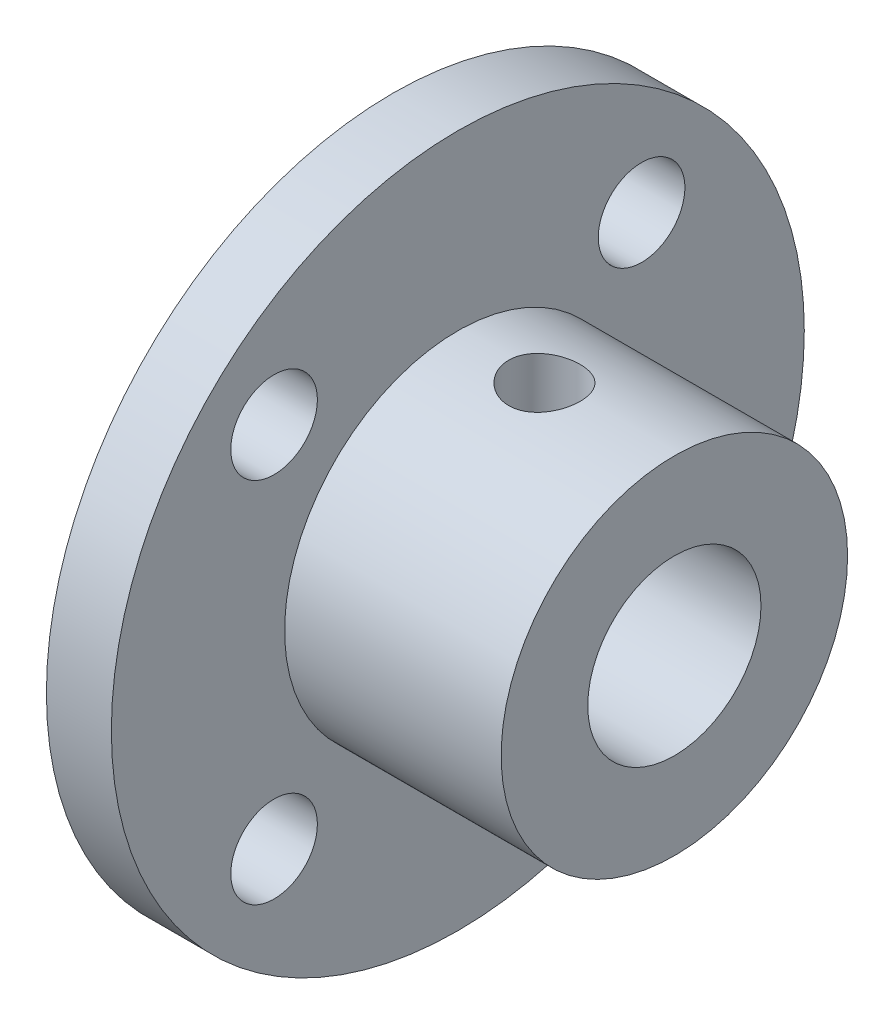
SolidWorks part; units mm, degrees
material "电镀钢"
ref_plane "前视基准面" through (0, 0, 0) normal (0, 0, 1) x (1, 0, 0)
ref_plane "上视基准面" through (0, 0, 0) normal (0, 1, 0) x (1, 0, 0)
ref_plane "右视基准面" through (0, 0, 0) normal (1, 0, 0) x (0, 0, -1)
sketch "草图1" plane through (0, 0, 0) normal (1, 0, 0) x (0, 0, -1)
  circle A0 centre (0, 0) radius 8
  circle A1 centre (0, 0) radius 4
  dimension "D1" = 8
  dimension "D2" = 16
extrude "凸台-拉伸1" add sketch "草图1" along normal blind 10
sketch "草图2" plane through (0, 0, 0) normal (-1, 0, 0) x (0, 0, 1)
  circle A0 centre (0, 0) radius 4
  circle A1 centre (0, 0) radius 16
  dimension "D1" = 32
  dimension "D2" = 8
extrude "凸台-拉伸2" add sketch "草图2" along normal blind 3
sketch "草图3" plane through (0, 0, 0) normal (1, 0, 0) x (0, 0, -1)
  line L0 (0, 0) -> (-8.9538, 8.9538) construction
  line L1 (0, 0) -> (-16.9706, -16.9706) construction
  line L2 (0, 0) -> (-19.7649, 0) construction
  circle A0 centre (-8.4853, -8.4853) radius 2
  circle A1 centre (8.4853, 8.4853) radius 2
  circle A2 centre (-8.4853, 8.4853) radius 2
  circle A3 centre (8.4853, -8.4853) radius 2
  dimension "D2" = 4
  dimension "D3" = 4
  dimension "D1" = 12
  dimension "D4" = 12
  dimension "D5" = 45
  dimension "D6" = 90
extrude "切除-拉伸1" cut sketch "草图3" against normal up to next
hole_wizard "M4 螺纹孔1" positions "草图4" profile "草图5" tap size "M4" standard "GB"
sketch "草图4" plane through (0, 0, 0) normal (0, 1, 0) x (1, 0, 0)
  point P0 (4.0004, 0)
sketch "草图5" plane through (4.0004, 0, 0) normal (1, 0, 0) x (0, 0, -1)
  line L0 (0, 0) -> (0, 12.4914)
  line L1 (0, 12.4914) -> (1.65, 11.5)
  line L2 (1.65, 11.5) -> (1.65, 0)
  line L5 (1.65, 0) -> (0, 0)
  line L10 (0, 12.4914) -> (-1.65, 11.5) construction
  line L11 (0, -6.35) -> (0, 107.95) construction
  dimension "螺纹孔钻头直径" = 3.3
  dimension "螺纹孔钻头深度" = 11.5
  dimension "导头角度" = 118
cosmetic thread "孔螺蚊线1" parameters "D1"=8, "D2"=4
